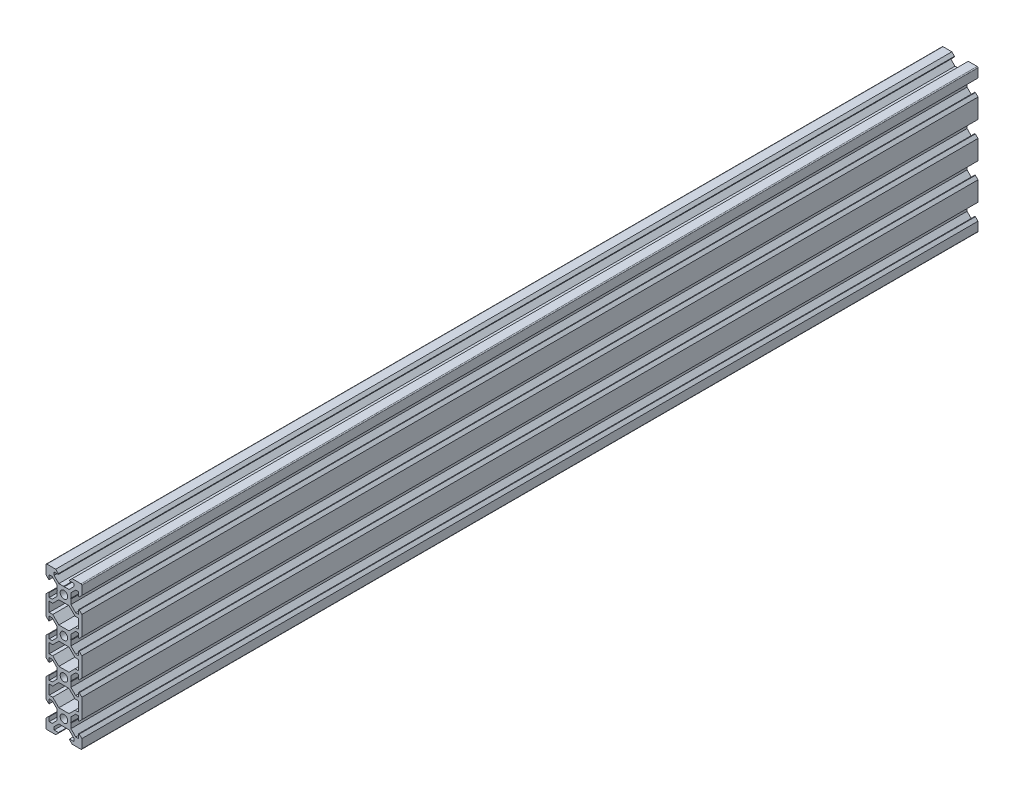
SolidWorks part; units mm, degrees
material "6061-T6 (SS)"
ref_plane "Front Plane" through (0, 0, 0) normal (0, 0, 1) x (1, 0, 0)
ref_plane "Top Plane" through (0, 0, 0) normal (0, 1, 0) x (1, 0, 0)
ref_plane "Right Plane" through (0, 0, 0) normal (1, 0, 0) x (0, 0, -1)
sketch "Sketch1" plane through (0, 0, 0) normal (0, 0, 1) x (1, 0, 0)
  line L0 (0, 0) -> (10, 0) construction
  line L1 (9.5, -40) -> (-9.5, -40)
  line L2 (10, -39.5) -> (10, 39.5)
  line L3 (9.5, 40) -> (-9.5, 40)
  line L4 (-10, -39.5) -> (-10, 39.5)
  line L5 (10, -40) -> (-10, 40) construction
  line L6 (10, 40) -> (-10, -40) construction
  circle A0 centre (0, 30) radius 2.1
  circle A1 centre (0, 10) radius 2.1
  circle A2 centre (0, -10) radius 2.1
  circle A3 centre (0, -30) radius 2.1
  arc A4 (-9.5, -40) -> (-10, -39.5) centre (-9.5, -39.5) cw
  arc A5 (9.5, -40) -> (10, -39.5) centre (9.5, -39.5) ccw
  arc A6 (10, 39.5) -> (9.5, 40) centre (9.5, 39.5) ccw
  arc A7 (-9.5, 40) -> (-10, 39.5) centre (-9.5, 39.5) ccw
  point P0 (0, 0)
  line B0 (0, 30) -> (0, 40) construction
  line B1 (0, 33.69) -> (-0.21, 33.9)
  line B2 (-0.21, 33.9) -> (-2.8393, 33.9)
  line B3 (-2.8393, 33.9) -> (-5.5, 36.5607)
  line B4 (-5.5, 36.5607) -> (-5.5, 38.2)
  line B5 (-5.5, 38.2) -> (-3.125, 38.2)
  line B6 (-3.125, 38.2) -> (-3.125, 38.545)
  line B7 (-3.125, 38.545) -> (-4.58, 40)
  line B8 (-4.58, 40) -> (4.58, 40)
  line B9 (0, 30) -> (-5.9132, 35.9132) construction
  line B10 (3.125, 38.545) -> (4.58, 40)
  line B11 (3.125, 38.2) -> (3.125, 38.545)
  line B12 (5.5, 38.2) -> (3.125, 38.2)
  line B13 (5.5, 36.5607) -> (5.5, 38.2)
  line B14 (2.8393, 33.9) -> (5.5, 36.5607)
  line B15 (0.21, 33.9) -> (2.8393, 33.9)
  line B16 (0, 33.69) -> (0.21, 33.9)
  line B17 (0, 30) -> (-10, 30) construction
  line B18 (-3.69, 30) -> (-3.9, 29.79)
  line B19 (-3.9, 29.79) -> (-3.9, 27.1607)
  line B20 (-3.9, 27.1607) -> (-6.5607, 24.5)
  line B21 (-6.5607, 24.5) -> (-8.2, 24.5)
  line B22 (-8.2, 24.5) -> (-8.2, 26.875)
  line B23 (-8.2, 26.875) -> (-8.545, 26.875)
  line B24 (-8.545, 26.875) -> (-10, 25.42)
  line B25 (-10, 25.42) -> (-10, 34.58)
  line B26 (0, 30) -> (-5.9132, 24.0868) construction
  line B27 (-8.545, 33.125) -> (-10, 34.58)
  line B28 (-8.2, 33.125) -> (-8.545, 33.125)
  line B29 (-8.2, 35.5) -> (-8.2, 33.125)
  line B30 (-6.5607, 35.5) -> (-8.2, 35.5)
  line B31 (-3.9, 32.8393) -> (-6.5607, 35.5)
  line B32 (-3.9, 30.21) -> (-3.9, 32.8393)
  line B33 (-3.69, 30) -> (-3.9, 30.21)
  line B34 (0, 10) -> (-10, 10) construction
  line B35 (-3.69, 10) -> (-3.9, 9.79)
  line B36 (-3.9, 9.79) -> (-3.9, 7.1607)
  line B37 (-3.9, 7.1607) -> (-6.5607, 4.5)
  line B38 (-6.5607, 4.5) -> (-8.2, 4.5)
  line B39 (-8.2, 4.5) -> (-8.2, 6.875)
  line B40 (-8.2, 6.875) -> (-8.545, 6.875)
  line B41 (-8.545, 6.875) -> (-10, 5.42)
  line B42 (-10, 5.42) -> (-10, 14.58)
  line B43 (0, 10) -> (-5.9132, 4.0868) construction
  line B44 (-8.545, 13.125) -> (-10, 14.58)
  line B45 (-8.2, 13.125) -> (-8.545, 13.125)
  line B46 (-8.2, 15.5) -> (-8.2, 13.125)
  line B47 (-6.5607, 15.5) -> (-8.2, 15.5)
  line B48 (-3.9, 12.8393) -> (-6.5607, 15.5)
  line B49 (-3.9, 10.21) -> (-3.9, 12.8393)
  line B50 (-3.69, 10) -> (-3.9, 10.21)
  line B51 (0, -10) -> (-10, -10) construction
  line B52 (-3.69, -10) -> (-3.9, -10.21)
  line B53 (-3.9, -10.21) -> (-3.9, -12.8393)
  line B54 (-3.9, -12.8393) -> (-6.5607, -15.5)
  line B55 (-6.5607, -15.5) -> (-8.2, -15.5)
  line B56 (-8.2, -15.5) -> (-8.2, -13.125)
  line B57 (-8.2, -13.125) -> (-8.545, -13.125)
  line B58 (-8.545, -13.125) -> (-10, -14.58)
  line B59 (-10, -14.58) -> (-10, -5.42)
  line B60 (0, -10) -> (-5.9132, -15.9132) construction
  line B61 (-8.545, -6.875) -> (-10, -5.42)
  line B62 (-8.2, -6.875) -> (-8.545, -6.875)
  line B63 (-8.2, -4.5) -> (-8.2, -6.875)
  line B64 (-6.5607, -4.5) -> (-8.2, -4.5)
  line B65 (-3.9, -7.1607) -> (-6.5607, -4.5)
  line B66 (-3.9, -9.79) -> (-3.9, -7.1607)
  line B67 (-3.69, -10) -> (-3.9, -9.79)
  line B68 (0, -30) -> (-10, -30) construction
  line B69 (-3.69, -30) -> (-3.9, -30.21)
  line B70 (-3.9, -30.21) -> (-3.9, -32.8393)
  line B71 (-3.9, -32.8393) -> (-6.5607, -35.5)
  line B72 (-6.5607, -35.5) -> (-8.2, -35.5)
  line B73 (-8.2, -35.5) -> (-8.2, -33.125)
  line B74 (-8.2, -33.125) -> (-8.545, -33.125)
  line B75 (-8.545, -33.125) -> (-10, -34.58)
  line B76 (-10, -34.58) -> (-10, -25.42)
  line B77 (0, -30) -> (-5.9132, -35.9132) construction
  line B78 (-8.545, -26.875) -> (-10, -25.42)
  line B79 (-8.2, -26.875) -> (-8.545, -26.875)
  line B80 (-8.2, -24.5) -> (-8.2, -26.875)
  line B81 (-6.5607, -24.5) -> (-8.2, -24.5)
  line B82 (-3.9, -27.1607) -> (-6.5607, -24.5)
  line B83 (-3.9, -29.79) -> (-3.9, -27.1607)
  line B84 (-3.69, -30) -> (-3.9, -29.79)
  line B85 (0, -30) -> (0, -40) construction
  line B86 (0, -33.69) -> (0.21, -33.9)
  line B87 (0.21, -33.9) -> (2.8393, -33.9)
  line B88 (2.8393, -33.9) -> (5.5, -36.5607)
  line B89 (5.5, -36.5607) -> (5.5, -38.2)
  line B90 (5.5, -38.2) -> (3.125, -38.2)
  line B91 (3.125, -38.2) -> (3.125, -38.545)
  line B92 (3.125, -38.545) -> (4.58, -40)
  line B93 (4.58, -40) -> (-4.58, -40)
  line B94 (0, -30) -> (5.9132, -35.9132) construction
  line B95 (-3.125, -38.545) -> (-4.58, -40)
  line B96 (-3.125, -38.2) -> (-3.125, -38.545)
  line B97 (-5.5, -38.2) -> (-3.125, -38.2)
  line B98 (-5.5, -36.5607) -> (-5.5, -38.2)
  line B99 (-2.8393, -33.9) -> (-5.5, -36.5607)
  line B100 (-0.21, -33.9) -> (-2.8393, -33.9)
  line B101 (0, -33.69) -> (-0.21, -33.9)
  line B102 (0, -30) -> (10, -30) construction
  line B103 (3.69, -30) -> (3.9, -29.79)
  line B104 (3.9, -29.79) -> (3.9, -27.1607)
  line B105 (3.9, -27.1607) -> (6.5607, -24.5)
  line B106 (6.5607, -24.5) -> (8.2, -24.5)
  line B107 (8.2, -24.5) -> (8.2, -26.875)
  line B108 (8.2, -26.875) -> (8.545, -26.875)
  line B109 (8.545, -26.875) -> (10, -25.42)
  line B110 (10, -25.42) -> (10, -34.58)
  line B111 (0, -30) -> (5.9132, -24.0868) construction
  line B112 (8.545, -33.125) -> (10, -34.58)
  line B113 (8.2, -33.125) -> (8.545, -33.125)
  line B114 (8.2, -35.5) -> (8.2, -33.125)
  line B115 (6.5607, -35.5) -> (8.2, -35.5)
  line B116 (3.9, -32.8393) -> (6.5607, -35.5)
  line B117 (3.9, -30.21) -> (3.9, -32.8393)
  line B118 (3.69, -30) -> (3.9, -30.21)
  line B119 (0, -10) -> (10, -10) construction
  line B120 (3.69, -10) -> (3.9, -9.79)
  line B121 (3.9, -9.79) -> (3.9, -7.1607)
  line B122 (3.9, -7.1607) -> (6.5607, -4.5)
  line B123 (6.5607, -4.5) -> (8.2, -4.5)
  line B124 (8.2, -4.5) -> (8.2, -6.875)
  line B125 (8.2, -6.875) -> (8.545, -6.875)
  line B126 (8.545, -6.875) -> (10, -5.42)
  line B127 (10, -5.42) -> (10, -14.58)
  line B128 (0, -10) -> (5.9132, -4.0868) construction
  line B129 (8.545, -13.125) -> (10, -14.58)
  line B130 (8.2, -13.125) -> (8.545, -13.125)
  line B131 (8.2, -15.5) -> (8.2, -13.125)
  line B132 (6.5607, -15.5) -> (8.2, -15.5)
  line B133 (3.9, -12.8393) -> (6.5607, -15.5)
  line B134 (3.9, -10.21) -> (3.9, -12.8393)
  line B135 (3.69, -10) -> (3.9, -10.21)
  line B136 (0, 10) -> (10, 10) construction
  line B137 (3.69, 10) -> (3.9, 10.21)
  line B138 (3.9, 10.21) -> (3.9, 12.8393)
  line B139 (3.9, 12.8393) -> (6.5607, 15.5)
  line B140 (6.5607, 15.5) -> (8.2, 15.5)
  line B141 (8.2, 15.5) -> (8.2, 13.125)
  line B142 (8.2, 13.125) -> (8.545, 13.125)
  line B143 (8.545, 13.125) -> (10, 14.58)
  line B144 (10, 14.58) -> (10, 5.42)
  line B145 (0, 10) -> (5.9132, 15.9132) construction
  line B146 (8.545, 6.875) -> (10, 5.42)
  line B147 (8.2, 6.875) -> (8.545, 6.875)
  line B148 (8.2, 4.5) -> (8.2, 6.875)
  line B149 (6.5607, 4.5) -> (8.2, 4.5)
  line B150 (3.9, 7.1607) -> (6.5607, 4.5)
  line B151 (3.9, 9.79) -> (3.9, 7.1607)
  line B152 (3.69, 10) -> (3.9, 9.79)
  line B153 (0, 30) -> (10, 30) construction
  line B154 (3.69, 30) -> (3.9, 30.21)
  line B155 (3.9, 30.21) -> (3.9, 32.8393)
  line B156 (3.9, 32.8393) -> (6.5607, 35.5)
  line B157 (6.5607, 35.5) -> (8.2, 35.5)
  line B158 (8.2, 35.5) -> (8.2, 33.125)
  line B159 (8.2, 33.125) -> (8.545, 33.125)
  line B160 (8.545, 33.125) -> (10, 34.58)
  line B161 (10, 34.58) -> (10, 25.42)
  line B162 (0, 30) -> (5.9132, 35.9132) construction
  line B163 (8.545, 26.875) -> (10, 25.42)
  line B164 (8.2, 26.875) -> (8.545, 26.875)
  line B165 (8.2, 24.5) -> (8.2, 26.875)
  line B166 (6.5607, 24.5) -> (8.2, 24.5)
  line B167 (3.9, 27.1607) -> (6.5607, 24.5)
  line B168 (3.9, 29.79) -> (3.9, 27.1607)
  line B169 (3.69, 30) -> (3.9, 29.79)
  line B170 (-8.2, 17.3) -> (-8.2, 22.7)
  line B171 (-8.2, 22.7) -> (-6.2393, 22.7)
  line B172 (-6.2393, 22.7) -> (-2.8393, 26.1)
  line B173 (-2.8393, 26.1) -> (2.8393, 26.1)
  line B174 (0, 26.1) -> (0, 20) construction
  line B175 (0, 20) -> (-8.2, 20) construction
  line B176 (6.2393, 22.7) -> (2.8393, 26.1)
  line B177 (8.2, 22.7) -> (6.2393, 22.7)
  line B178 (8.2, 17.3) -> (8.2, 22.7)
  line B179 (8.2, 17.3) -> (6.2393, 17.3)
  line B180 (6.2393, 17.3) -> (2.8393, 13.9)
  line B181 (-2.8393, 13.9) -> (2.8393, 13.9)
  line B182 (-6.2393, 17.3) -> (-2.8393, 13.9)
  line B183 (-8.2, 17.3) -> (-6.2393, 17.3)
  line B184 (0, 26.1) -> (0, 30) construction
  line B185 (0, 30) -> (-5.0927, 24.9073) construction
  line B186 (-8.2, -2.7) -> (-8.2, 2.7)
  line B187 (-8.2, 2.7) -> (-6.2393, 2.7)
  line B188 (-6.2393, 2.7) -> (-2.8393, 6.1)
  line B189 (-2.8393, 6.1) -> (2.8393, 6.1)
  line B190 (0, 6.1) -> (0, 0) construction
  line B191 (0, 0) -> (-8.2, 0) construction
  line B192 (6.2393, 2.7) -> (2.8393, 6.1)
  line B193 (8.2, 2.7) -> (6.2393, 2.7)
  line B194 (8.2, -2.7) -> (8.2, 2.7)
  line B195 (8.2, -2.7) -> (6.2393, -2.7)
  line B196 (6.2393, -2.7) -> (2.8393, -6.1)
  line B197 (-2.8393, -6.1) -> (2.8393, -6.1)
  line B198 (-6.2393, -2.7) -> (-2.8393, -6.1)
  line B199 (-8.2, -2.7) -> (-6.2393, -2.7)
  line B200 (0, 6.1) -> (0, 10) construction
  line B201 (0, 10) -> (-5.0927, 4.9073) construction
  line B202 (-8.2, -22.7) -> (-8.2, -17.3)
  line B203 (-8.2, -17.3) -> (-6.2393, -17.3)
  line B204 (-6.2393, -17.3) -> (-2.8393, -13.9)
  line B205 (-2.8393, -13.9) -> (2.8393, -13.9)
  line B206 (0, -13.9) -> (0, -20) construction
  line B207 (0, -20) -> (-8.2, -20) construction
  line B208 (6.2393, -17.3) -> (2.8393, -13.9)
  line B209 (8.2, -17.3) -> (6.2393, -17.3)
  line B210 (8.2, -22.7) -> (8.2, -17.3)
  line B211 (8.2, -22.7) -> (6.2393, -22.7)
  line B212 (6.2393, -22.7) -> (2.8393, -26.1)
  line B213 (-2.8393, -26.1) -> (2.8393, -26.1)
  line B214 (-6.2393, -22.7) -> (-2.8393, -26.1)
  line B215 (-8.2, -22.7) -> (-6.2393, -22.7)
  line B216 (0, -13.9) -> (0, -10) construction
  line B217 (0, -10) -> (-5.0927, -15.0927) construction
sketch_block_instance "V Slot 1-4"
sketch_block "V Slot 1" parameters "D1"=10, "D2"=11, "D3"=4.3, "D4"=1.8, "D5"=0.21, "D6"=45, "D7"=9.16, "D8"=1.5, "D9"=6.25
sketch_block_instance "V Slot 1-5"
sketch_block_instance "V Slot 1-6"
sketch_block_instance "V Slot 1-7"
sketch_block_instance "V Slot 1-8"
sketch_block_instance "V Slot 1-9"
sketch_block_instance "V Slot 1-10"
sketch_block_instance "V Slot 1-11"
sketch_block_instance "V Slot 1-12"
sketch_block_instance "V Slot 1-13"
sketch_block_instance "Center Cutout 1-1"
sketch_block "Center Cutout 1" parameters "D1"=5.4, "D2"=12.2, "D3"=8.2, "D4"=45, "D5"=10, "D6"=1.5
sketch_block_instance "Center Cutout 1-2"
sketch_block_instance "Center Cutout 1-3" parameters "D5"=5.9516, "D6"=0.5, "D1"=53.3893, "D2"=54.3269, "D3"=11.952, "D4"=27.681
extrude "Boss-Extrude1" add sketch "Sketch1" along normal blind 500 contours B169 B154 B155 B156 B157 B158 B159 B160 L2 A6 L3 B10 B11 B12 B13 B14 B15 B16 B1 B2 B3 B4 B5 B6 B7 A7 L4 B27 B28 B29 B30 B31 B32 B33 B18 B19 B20 B21 B22 B23 B24 B44 B45 B46 B47 B48 B49 B50 B35
